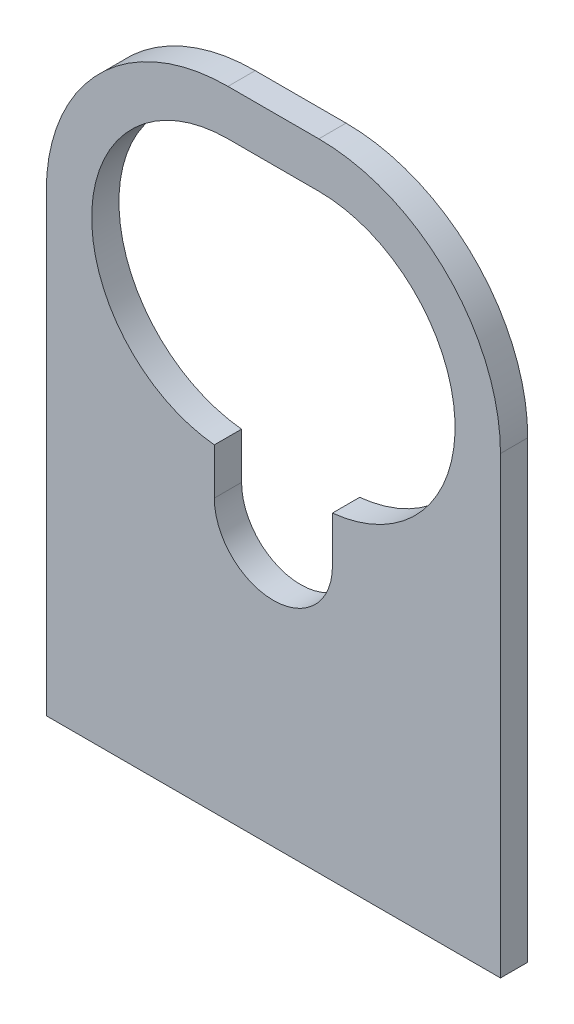
SolidWorks part; units mm, degrees
ref_plane "Front Plane" through (0, 0, 0) normal (0, 0, 1) x (1, 0, 0)
ref_plane "Top Plane" through (0, 0, 0) normal (0, 1, 0) x (1, 0, 0)
ref_plane "Right Plane" through (0, 0, 0) normal (1, 0, 0) x (0, 0, -1)
sketch "Sketch1" plane through (0, 0, 0) normal (0, 0, 1) x (1, 0, 0)
  line L1 (-25, 40) -> (25, 40)
  line L2 (-25, 40) -> (-25, -30)
  line L3 (-25, -30) -> (25, -30)
  line L4 (25, 40) -> (25, -30)
  point P8 (0, -30)
  dimension "D1" = 30
  dimension "D2" = 50
  dimension "D3" = 40
extrude "Boss-Extrude1" add sketch "Sketch1" along normal blind 3
sketch "Sketch2" plane through (0, 0, 3) normal (0, 0, 1) x (1, 0, 0)
  circle A0 centre (0, 0) radius 6.5
  dimension "D1" = 13
extrude "Cut-Extrude1" cut sketch "Sketch2" against normal through all both and the other way through all
sketch "Sketch3" plane through (0, 0, 3) normal (0, 0, 1) x (1, 0, 0)
  line L0 (-5, 20) -> (5, 20) construction
  line L1 (-5, 35) -> (5, 35)
  line L2 (-5, 5) -> (5, 5)
  arc A0 (-5, 35) -> (-5, 5) centre (-5, 20) ccw
  arc A1 (5, 5) -> (5, 35) centre (5, 20) ccw
  point P2 (0, 20)
  point P13 (-20, 20)
  point P14 (20, 20)
  dimension "D2" = 40
  dimension "D1" = 30
  dimension "D3" = 20
extrude "Cut-Extrude2" cut sketch "Sketch3" against normal through all both and the other way through all
sketch "Sketch4" plane through (0, 0, 3) normal (0, 0, 1) x (1, 0, 0)
  line L1 (-6.5, 0) -> (6.5, 0)
  line L2 (-6.5, 0) -> (-6.5, 15)
  line L3 (-6.5, 15) -> (6.5, 15)
  line L4 (6.5, 0) -> (6.5, 15)
  circle A0 centre (0, 0) radius 6.5 construction
  dimension "D1" = 15
extrude "Cut-Extrude3" cut sketch "Sketch4" against normal through all both and the other way through all
fillet "Fillet1" radius 20 2 edges at (25, 40, 1.5) (-25, 40, 1.5)
